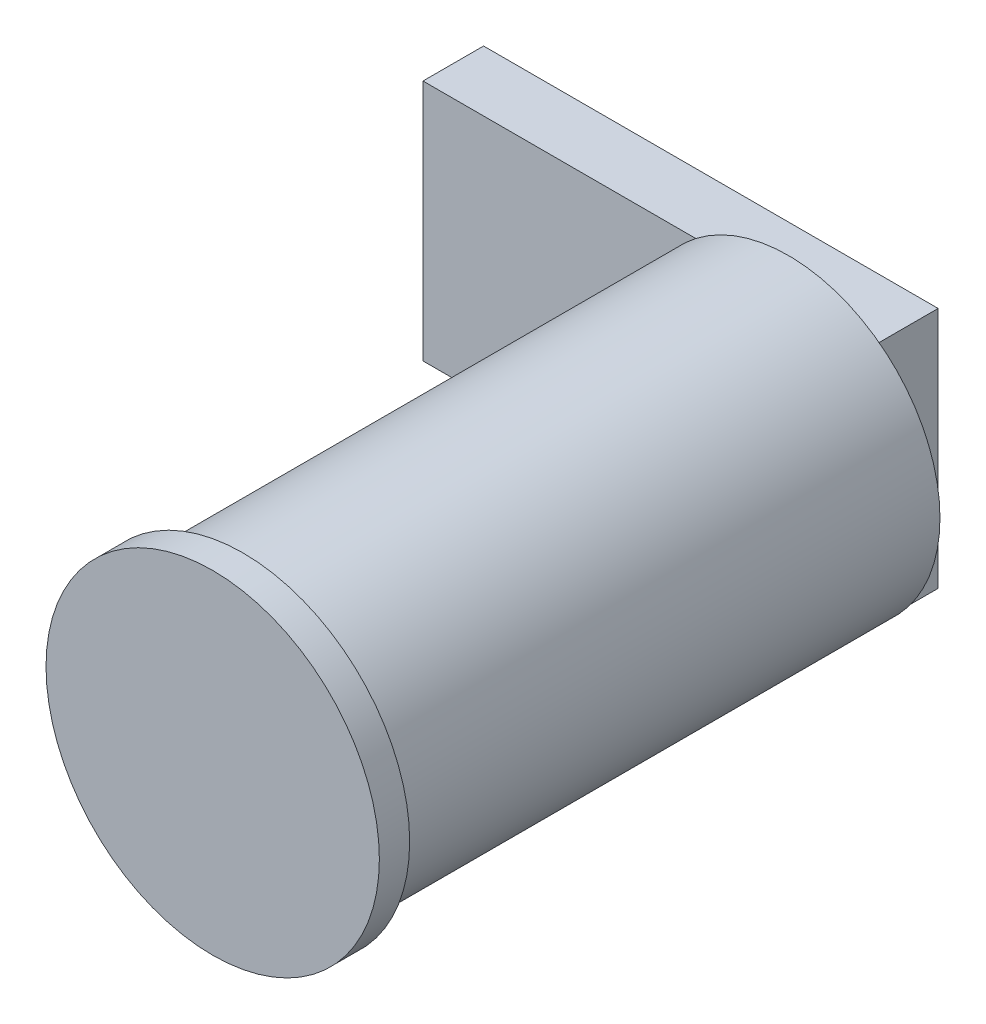
SolidWorks part; units mm, degrees
ref_plane "Plan de face" through (0, 0, 0) normal (0, 0, 1) x (1, 0, 0)
ref_plane "Plan de dessus" through (0, 0, 0) normal (0, 1, 0) x (1, 0, 0)
ref_plane "Plan de droite" through (0, 0, 0) normal (1, 0, 0) x (0, 0, -1)
sketch "Esquisse1" plane through (0, 0, 0) normal (0, 0, 1) x (1, 0, 0)
  circle A0 centre (0, 0) radius 5.5
  circle A1 centre (0, 0) radius 5
  dimension "D1" = 11
extrude "Boss.-Extru.1" add sketch "Esquisse1" against normal blind 1
sketch "Esquisse4" plane through (0, 0, 0) normal (0, 0, 1) x (1, 0, 0)
  circle A0 centre (0, 0) radius 5
extrude "Boss.-Extru.2" add sketch "Esquisse4" against normal blind 19
sketch "Esquisse5" plane through (0, 0, -19) normal (0, 0, -1) x (-1, 0, 0)
  line L1 (-2.9392, -4.0449) -> (12.0608, -4.0449)
  line L2 (-2.9392, -4.0449) -> (-2.9392, 3.9558)
  line L3 (-2.9392, 3.9558) -> (12.0608, 3.9558)
  line L4 (12.0608, -4.0449) -> (12.0608, 3.9558)
  circle A0 centre (0, 0) radius 5 construction
  dimension "D1" = 15
extrude "Boss.-Extru.3" add sketch "Esquisse5" along normal blind 2
